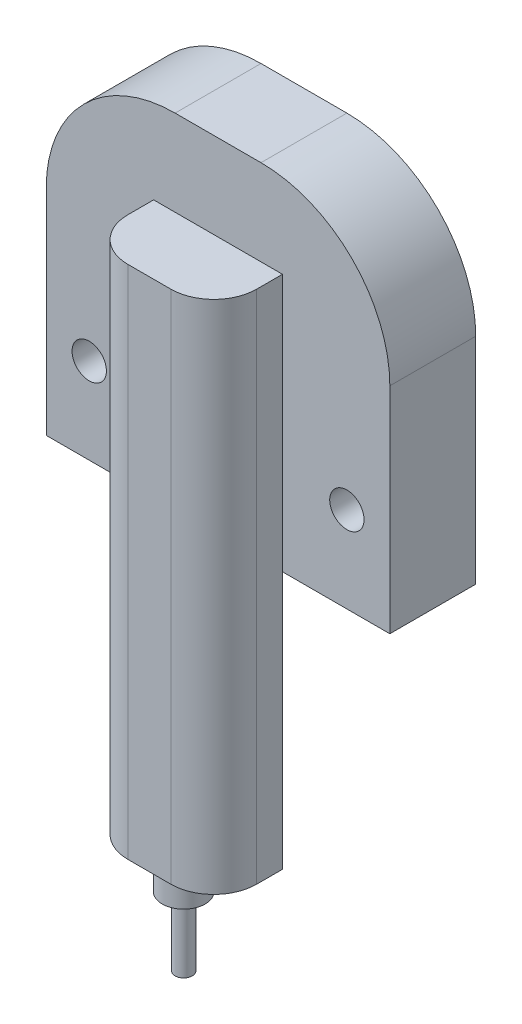
SolidWorks part; units mm, degrees
ref_plane "Front Plane" through (0, 0, 0) normal (0, 0, 1) x (1, 0, 0)
ref_plane "Top Plane" through (0, 0, 0) normal (0, 1, 0) x (1, 0, 0)
ref_plane "Right Plane" through (0, 0, 0) normal (1, 0, 0) x (0, 0, -1)
sketch "Sketch1" plane through (0, 0, 0) normal (0, 1, 0) x (1, 0, 0)
  line L1 (-20, 5) -> (20, 5)
  line L2 (-20, 5) -> (-20, -5)
  line L3 (-20, -5) -> (20, -5)
  line L4 (20, 5) -> (20, -5)
  line L5 (-20, 5) -> (20, -5) construction
  line L6 (-20, -5) -> (20, 5) construction
  point P0 (0, 0)
  dimension "D1" = 10
  dimension "D2" = 40
extrude "Boss-Extrude1" add sketch "Sketch1" along normal blind 40
fillet "Fillet1" radius 15 2 edges at (-20, 40, 0) (20, 40, 0)
sketch "Sketch3" plane through (0, 0, 5) normal (0, 0, 1) x (1, 0, 0)
  line L0 (20, 25) -> (20, 0) construction
  line L1 (-20, 10) -> (20, 10) construction
  line L2 (-20, 25) -> (-20, 0) construction
  line L3 (-20, 0) -> (20, 0) construction
  circle A0 centre (15, 10) radius 2
  circle A1 centre (-15, 10) radius 2
  dimension "D1" = 4
  dimension "D4" = 4
  dimension "D2" = 5
  dimension "D3" = 10
  dimension "D5" = 5
extrude "Cut-Extrude1" cut sketch "Sketch3" against normal blind 10
sketch "Sketch7" plane through (0, 0, 5) normal (0, 0, 1) x (1, 0, 0)
  line L1 (-7.5, -30) -> (7.5, -30)
  line L2 (-7.5, -30) -> (-7.5, 30)
  line L3 (-7.5, 30) -> (7.5, 30)
  line L4 (7.5, -30) -> (7.5, 30)
  line L5 (-7.5, -30) -> (7.5, 30) construction
  line L6 (-7.5, 30) -> (7.5, -30) construction
  point P0 (0, 0)
  dimension "D1" = 15
  dimension "D2" = 60
extrude "Boss-Extrude5" add sketch "Sketch7" along normal blind 8
sketch "Sketch8" plane through (0, -30, 0) normal (0, -1, 0) x (1, 0, 0)
  line L0 (-7.5, 13) -> (7.5, 13) construction
  line L1 (-7.5, 13) -> (-7.5, 5) construction
  circle A0 centre (0, 9) radius 2.5
  point P2 (0, 13)
  point P5 (-7.5, 9)
  dimension "D3" = 5
  dimension "D1" = 4
  dimension "D2" = 7.5
extrude "Boss-Extrude6" add sketch "Sketch8" along normal blind 4
sketch "Sketch9" plane through (0, -34, 0) normal (0, -1, 0) x (1, 0, 0)
  circle A0 centre (0, 9) radius 1
  dimension "D1" = 2
extrude "Boss-Extrude7" add sketch "Sketch9" along normal blind 8
fillet "Fillet3" radius 5 2 edges at (-7.5, 0, 13) (7.5, 0, 13)
